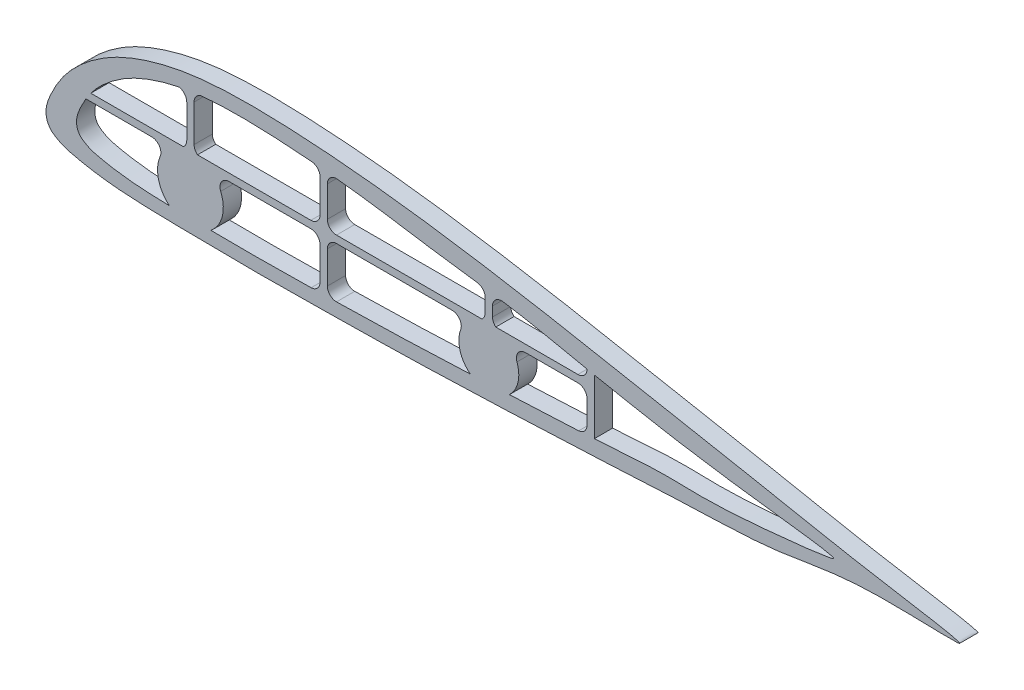
SolidWorks part; units mm, degrees
material "Cedar"
ref_plane "Front Plane" through (0, 0, 0) normal (0, 0, 1) x (1, 0, 0)
ref_plane "Top Plane" through (0, 0, 0) normal (0, 1, 0) x (1, 0, 0)
ref_plane "Right Plane" through (0, 0, 0) normal (1, 0, 0) x (0, 0, -1)
sketch "Sketch2" plane through (0, 0, 0) normal (0, 0, 1) x (1, 0, 0)
  line L0 (-169.9991, 24.7191) -> (-169.9991, 4.5442)
  line L1 (-173.9991, 22.7895) -> (-173.9991, 4.5442)
  line L2 (-175.8813, 0.6353) -> (-226.5288, 0.6353)
  line L3 (-229.2133, -3.3647) -> (-193.1651, -3.3647)
  line L4 (-150.8331, -3.3647) -> (-106.0494, -3.3647)
  line L5 (-101.0494, -26.252) -> (-101.0494, -8.3647)
  line L6 (-97.0494, -26.0263) -> (-97.0494, -8.3647)
  line L7 (-92.0494, -3.3647) -> (-28.7339, -3.3647)
  line L8 (11.4388, -3.3647) -> (40.1029, -3.3647)
  line L9 (45.1029, -8.3647) -> (45.1029, -20.8742)
  line L10 (49.1029, 4.8853) -> (49.1029, -25.315)
  line L11 (40.1029, 0.6353) -> (-4.8432, 0.6353)
  line L12 (-6.6502, 4.4831) -> (-6.6502, 9.6919)
  line L13 (-10.6541, 11.6916) -> (-10.6541, 4.4581)
  line L14 (-12.4313, 0.6353) -> (-92.0494, 0.6353)
  line L15 (-97.0494, 5.6353) -> (-97.0494, 22.4075)
  line L16 (-101.0494, 5.6353) -> (-101.0494, 23.721)
  line L17 (-106.0494, 0.6353) -> (-168.1169, 0.6353)
  arc A0 (-166.3333, 29.5378) -> (-169.9991, 24.7191) centre (-164.9991, 24.7191) ccw
  arc A1 (-169.9991, 4.5442) -> (-168.1169, 0.6353) centre (-164.9991, 4.5442) ccw
  arc A2 (-173.9991, 22.7895) -> (-178.2312, 27.7302) centre (-179.1316, 22.676) ccw
  arc A3 (-175.8813, 0.6353) -> (-173.9991, 4.5442) centre (-178.9991, 4.5442) ccw
  arc A4 (-188.5638, -10.3212) -> (-193.1651, -3.3647) centre (-193.1651, -8.3647) ccw
  arc A5 (-188.5638, -10.3212) -> (-183.5467, -31.1724) centre (-171.9991, -17.3647) ccw
  arc A6 (-160.8663, -31.509) -> (-155.4344, -10.3212) centre (-171.9991, -17.3647) ccw
  arc A7 (-150.8331, -3.3647) -> (-155.4344, -10.3212) centre (-150.8331, -8.3647) ccw
  arc A8 (-101.0494, -8.3647) -> (-106.0494, -3.3647) centre (-106.0494, -8.3647) ccw
  arc A9 (-105.8986, -31.2497) -> (-101.0494, -26.252) centre (-106.0494, -26.252) ccw
  arc A10 (-97.0494, -26.0263) -> (-92.0494, -31.0263) centre (-92.0494, -26.0263) ccw
  arc A11 (-92.0494, -3.3647) -> (-97.0494, -8.3647) centre (-92.0494, -8.3647) ccw
  arc A12 (-24.0424, -10.0937) -> (-28.7339, -3.3647) centre (-28.7339, -8.3647) ccw
  arc A13 (-24.0424, -10.0937) -> (-18.8229, -28.6315) centre (-8.6541, -15.7647) ccw
  arc A14 (2.5986, -27.6738) -> (6.7451, -10.0878) centre (-8.6502, -15.7397) ccw
  arc A15 (11.4388, -3.3647) -> (6.7451, -10.0878) centre (11.4388, -8.3647) ccw
  arc A16 (45.1029, -8.3647) -> (40.1029, -3.3647) centre (40.1029, -8.3647) ccw
  arc A17 (40.53, -25.8559) -> (45.1029, -20.8742) centre (40.1029, -20.8742) ccw
  arc A18 (40.1029, 0.6353) -> (45.1024, 5.6999) centre (40.1029, 5.6353) ccw
  arc A19 (-6.6502, 4.4831) -> (-4.8432, 0.6353) centre (-1.6502, 4.4831) ccw
  arc A20 (-0.8909, 14.6339) -> (-6.6502, 9.6919) centre (-1.6502, 9.6919) ccw
  arc A21 (-10.6541, 11.6916) -> (-14.9834, 16.6464) centre (-15.6541, 11.6916) ccw
  arc A22 (-12.4313, 0.6353) -> (-10.6541, 4.4581) centre (-15.6541, 4.4581) ccw
  arc A23 (-97.0494, 5.6353) -> (-92.0494, 0.6353) centre (-92.0494, 5.6353) ccw
  arc A24 (-101.0494, 23.721) -> (-105.2218, 28.6521) centre (-106.0494, 23.721) ccw
  arc A25 (-106.0494, 0.6353) -> (-101.0494, 5.6353) centre (-106.0494, 5.6353) ccw
  arc A26 (-92.0494, 27.4075) -> (-97.0494, 22.4075) centre (-92.0494, 22.4075) ccw
  spline S0 degree 3 poles (245.9221, -23.3374) (252.2731, -21.4938) (191.2193, -11.9146) (151.2129, -3.5337) (98.5312, 6.2467) (49.2937, 15.7383) (-0.816, 24.9435) (-50.7364, 32.5697) (-92.4924, 36.9876) (-125.881, 38.7935) (-150.9432, 38.979) (-176.2395, 36.8572) (-198.1362, 31.2855) (-214.7696, 24.0209) (-226.4289, 16.404) (-234.7631, 9.2099) (-241.3618, 1.6224) (-245.4471, -4.7125) (-249.3441, -12.5517) (-252.2731, -20.3607) (-249.2876, -27.2304) (-245.2592, -30.0668) (-241.0959, -32.2025) (-234.2743, -33.8725) (-225.9573, -35.5581) (-214.2702, -37.1046) (-197.5861, -38.217) (-175.9009, -38.562) (-150.9011, -38.8904) (-125.8981, -38.979) (-92.5666, -38.4685) (-50.8769, -37.8945) (-0.9311, -36.0401) (49.2607, -33.9459) (98.5366, -30.9769) (151.3512, -29.9449) (189.8638, -19.9396) (245.9221, -23.3374) (252.2731, -21.4938) (191.2193, -11.9146) knots -0.096715 -0.048179 -0.004818 0 0.049041 0.098082 0.147123 0.196163 0.245117 0.293835 0.342264 0.366386 0.390475 0.414675 0.439566 0.455415 0.466908 0.479712 0.48709 0.495937 0.501323 0.512663 0.51831 0.521365 0.526752 0.531755 0.541582 0.551305 0.565797 0.589895 0.613986 0.638076 0.662167 0.710354 0.75856 0.806786 0.855025 0.903285 0.951821 0.995182 1 1.049041 1.098082 1.147123 only from (249.1003, -22.3005) to (249.1003, -22.3005)
  spline S1 degree 3 poles (-160.8663, -31.509) (-158.6558, -31.5336) (-149.7791, -31.6217) (-134.2332, -31.6766) (-118.1246, -31.4309) (-108.6774, -31.2916) (-105.8986, -31.2497) knots 0.606033 0.606033 0.606033 0.606033 0.614021 0.638112 0.662205 0.672244 0.672244 0.672244 0.672244
  spline S2 degree 3 poles (-92.0494, -31.0263) (-86.1083, -30.9216) (-66.833, -30.5334) (-42.502, -29.6636) (-23.9575, -28.8588) (-18.8229, -28.6315) knots 0.688924 0.688924 0.688924 0.688924 0.710394 0.758604 0.777109 0.777109 0.777109 0.777109
  spline S3 degree 3 poles (2.5986, -27.6738) (3.6559, -27.6269) (16.2407, -27.0711) (28.5724, -26.5611) (40.53, -25.8559) knots 0.802973 0.802973 0.802973 0.802973 0.806832 0.848975 0.848975 0.848975 0.848975
  spline S4 degree 3 poles (49.1029, -25.315) (62.0521, -24.4479) (92.8792, -21.9847) (111.4399, -25.1616) (176.2325, -18.1628) (179.9352, -16.7853) (180.0199, -16.6325) (180.9646, -14.9296) (138.7474, -10.5694) (99.4843, -4.2413) (101.2387, -4.9609) (65.2014, 1.6352) (49.1029, 4.8853) knots 0.858908 0.858908 0.858908 0.858908 0.903337 0.960407 0.996041 1 1 1 1.044139 1.053948 1.098087 1.147128 1.147128 1.147128 1.147128
  spline S5 degree 3 poles (45.1024, 5.6999) (30.7772, 8.6397) (16.2804, 11.8868) (1.5182, 14.2637) (-0.8909, 14.6339) knots 0.151251 0.151251 0.151251 0.151251 0.196175 0.204915 0.204915 0.204915 0.204915
  spline S6 degree 3 poles (-14.9834, 16.6464) (-21.411, 17.5165) (-41.3358, 20.1029) (-66.7693, 24.4639) (-86.0967, 26.7816) (-92.0494, 27.4075) knots 0.221911 0.221911 0.221911 0.221911 0.245131 0.293851 0.315473 0.315473 0.315473 0.315473
  spline S7 degree 3 poles (-105.2218, 28.6521) (-108.2248, 28.9043) (-117.8898, 29.6477) (-134.2187, 30.5447) (-151.6115, 30.6696) (-162.3132, 29.9664) (-166.3333, 29.5378) knots 0.331401 0.331401 0.331401 0.331401 0.342283 0.366407 0.390497 0.405098 0.405098 0.405098 0.405098
  spline S8 degree 3 poles (-178.2312, 27.7302) (-183.6636, 26.6349) (-193.2696, 23.9907) (-205.3306, 18.7231) (-214.6581, 12.6296) (-221.3254, 6.8743) (-225.1025, 2.5312) (-226.4314, 0.7661) (-226.5288, 0.6353) knots 0.419589 0.419589 0.419589 0.419589 0.439591 0.455441 0.466935 0.479739 0.487118 0.487706 0.487706 0.487706 0.487706
  spline S9 degree 3 poles (-229.2133, -3.3647) (-229.5661, -3.9489) (-230.6504, -5.8282) (-232.9903, -10.535) (-235.3335, -16.7822) (-232.945, -22.278) (-229.7223, -24.5471) (-226.3917, -26.2556) (-220.9344, -27.5916) (-214.2808, -28.9401) (-204.9311, -30.1773) (-194.6827, -30.8606) (-187.1107, -31.0926) (-183.5467, -31.1724) knots 0.493499 0.493499 0.493499 0.493499 0.495965 0.501352 0.512693 0.51834 0.521395 0.526782 0.531785 0.541613 0.551336 0.56583 0.578711 0.578711 0.578711 0.578711
extrude "Boss-Extrude1" add sketch "Sketch2" along normal blind 10
sketch "Sketch3" plane through (0, 0, 0) normal (0, 1, 0) x (1, 0, 0)
  line L0 (-251.0494, -5) -> (-251.0494, 9.5472) construction
  line L1 (-251.0494, 0) -> (-251.0494, -10) construction
